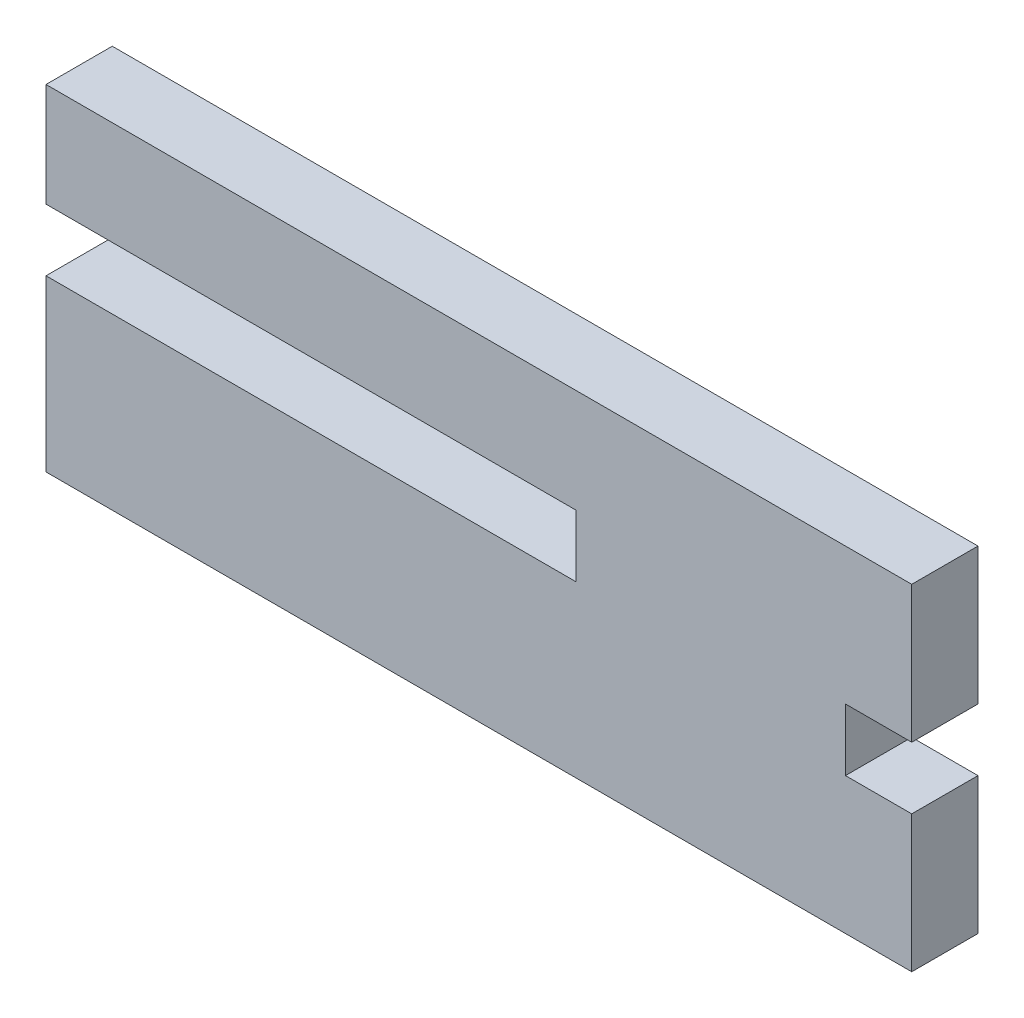
SolidWorks part; units mm, degrees
ref_plane "Front Plane" through (0, 0, 0) normal (0, 0, 1) x (1, 0, 0)
ref_plane "Top Plane" through (0, 0, 0) normal (0, 1, 0) x (1, 0, 0)
ref_plane "Right Plane" through (0, 0, 0) normal (1, 0, 0) x (0, 0, -1)
sketch "Sketch1" plane through (0, 0, 0) normal (0, 0, 1) x (1, 0, 0)
  line L0 (41.275, 6.35) -> (41.275, 0) construction
  line L1 (0, 0) -> (25.4, 0) construction
  line L2 (0, 0) -> (0, 4.7625) construction
  line L3 (0, 15.875) -> (25.4, 15.875) construction
  line L5 (0, 11.1125) -> (25.4, 11.1125) construction
  line L6 (0, 11.1125) -> (0, 4.7625) construction
  line L7 (0, 4.7625) -> (25.4, 4.7625) construction
  line L8 (25.4, 11.1125) -> (25.4, 7.9375) construction
  line L9 (25.4, 15.875) -> (41.275, 15.875) construction
  line L10 (25.4, 11.1125) -> (25.4, 7.9375)
  line L11 (25.4, 0) -> (41.275, 0) construction
  line L12 (0, 4.7625) -> (0, 11.1125) construction
  line L13 (0, 11.1125) -> (0, 15.875) construction
  line L14 (25.4, 11.1125) -> (25.4, 7.9375)
  line L15 (0, 4.7625) -> (25.4, 4.7625) construction
  line L16 (0, 4.7625) -> (0, 7.9375) construction
  line L17 (0, 7.9375) -> (25.4, 7.9375) construction
  line L18 (25.4, 4.7625) -> (25.4, 7.9375) construction
  line L19 (41.275, 15.875) -> (41.275, 9.525) construction
  line L20 (28.575, 9.525) -> (36.5125, 9.525) construction
  line L21 (28.575, 9.525) -> (28.575, 6.35) construction
  line L22 (28.575, 6.35) -> (36.5125, 6.35) construction
  line L23 (36.5125, 9.525) -> (36.5125, 6.35) construction
  line L24 (38.1, 9.525) -> (41.275, 9.525) construction
  line L25 (38.1, 9.525) -> (38.1, 6.35) construction
  line L26 (38.1, 6.35) -> (41.275, 6.35) construction
  line L27 (25.4, 7.9375) -> (25.4, 4.7625) construction
  line L28 (25.4, 7.9375) -> (25.4, 4.7625) construction
  line L29 (25.4, 7.9375) -> (25.4, 4.7625) construction
  line L30 (-0.1016, 15.9766) -> (25.4, 15.9766)
  line L31 (25.4, 15.9766) -> (41.3766, 15.9766)
  line L32 (41.3766, 15.9766) -> (41.3766, 9.4234)
  line L33 (38.2016, 9.4234) -> (41.3766, 9.4234)
  line L34 (38.2016, 9.4234) -> (38.2016, 6.4516)
  line L35 (38.2016, 6.4516) -> (41.3766, 6.4516)
  line L36 (41.3766, 6.4516) -> (41.3766, -0.1016)
  line L37 (25.4, -0.1016) -> (41.3766, -0.1016)
  line L38 (-0.1016, -0.1016) -> (25.4, -0.1016)
  line L39 (-0.1016, -0.1016) -> (-0.1016, 4.7625)
  line L40 (-0.1016, 4.7625) -> (-0.1016, 8.0391)
  line L41 (-0.1016, 8.0391) -> (25.2984, 8.0391)
  line L42 (25.2984, 11.0109) -> (25.2984, 8.0391)
  line L43 (-0.1016, 11.0109) -> (25.2984, 11.0109)
  line L44 (-0.1016, 11.0109) -> (-0.1016, 15.9766)
  line L45 (28.6766, 9.4234) -> (28.6766, 6.4516)
  line L46 (28.6766, 6.4516) -> (36.4109, 6.4516)
  line L47 (36.4109, 9.4234) -> (36.4109, 6.4516)
  line L48 (28.6766, 9.4234) -> (36.4109, 9.4234)
  point P21 (38.1, 7.9375)
  dimension "D5" = 7.9375
  dimension "D6" = 3.175
  dimension "D1" = 15.875
  dimension "D2" = 6.35
  dimension "D3" = 25.4
  dimension "D4" = 15.875
  dimension "D7" = 1.5875
  dimension "D8" = 3.175
  dimension "D9" = 7.9375
  dimension "D10" = 0.1016
  dimension "D11" = 0.1016
extrude "Boss-Extrude1" add sketch "Sketch1" along normal blind 3.175
